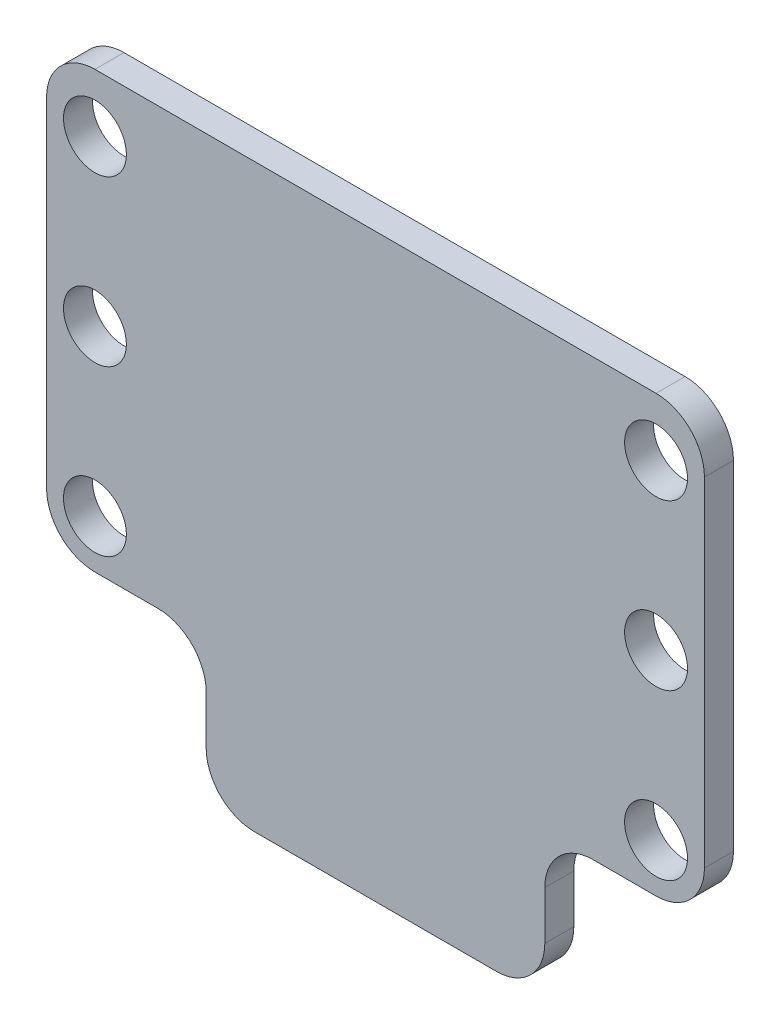
SolidWorks part; units mm, degrees
ref_plane "Plan de face" through (0, 0, 0) normal (0, 0, 1) x (1, 0, 0)
ref_plane "Plan de dessus" through (0, 0, 0) normal (0, 1, 0) x (1, 0, 0)
ref_plane "Plan de droite" through (0, 0, 0) normal (1, 0, 0) x (0, 0, -1)
sketch "Esquisse2" plane through (0, 0, 0) normal (0, 0, 1) x (1, 0, 0)
  line L0 (39.2085, -84.0985) -> (39.2085, -5.0985) construction
  line L1 (107.2085, 1.9015) -> (39.2085, 1.9015)
  line L2 (107.2085, 1.9015) -> (107.2085, -43.0985)
  line L3 (107.2085, -43.0985) -> (90.7085, -43.0985)
  line L4 (39.2085, 1.9015) -> (39.2085, -43.0985)
  line L5 (55.7085, -43.0985) -> (39.2085, -43.0985)
  line L7 (90.7085, -43.0985) -> (90.7085, -58.0985)
  line L8 (90.7085, -58.0985) -> (55.7085, -58.0985)
  line L9 (55.7085, -43.0985) -> (55.7085, -58.0985)
  circle A0 centre (102.2085, -4.0985) radius 3.25
  circle A1 centre (102.2085, -38.0985) radius 3.25
  circle A2 centre (44.2085, -38.0985) radius 3.25
  circle A3 centre (44.2085, -4.0985) radius 3.25
  circle A4 centre (44.2085, -21.0985) radius 3.25
  circle A5 centre (102.2085, -21.0985) radius 3.25
  point P23 (73.2085, -58.0985)
  point P24 (73.2085, 1.9015)
  point P27 (0, 0)
  point P30 (0, 0)
  dimension "D4" = 6.5
  dimension "D1" = 45
  dimension "D2" = 15
  dimension "D3" = 35
  dimension "D5" = 17
extrude "Boss.-Extru.1" add sketch "Esquisse2" along normal blind 3
fillet "Congé1" radius 5 8 edges at (39.2085, 1.9015, 1.5) (39.2085, -43.0985, 1.5) (55.7085, -58.0985, 1.5) (55.7085, -43.0985, 1.5) (90.7085, -58.0985, 1.5) (90.7085, -43.0985, 1.5) (107.2085, -43.0985, 1.5) (107.2085, 1.9015, 1.5)
